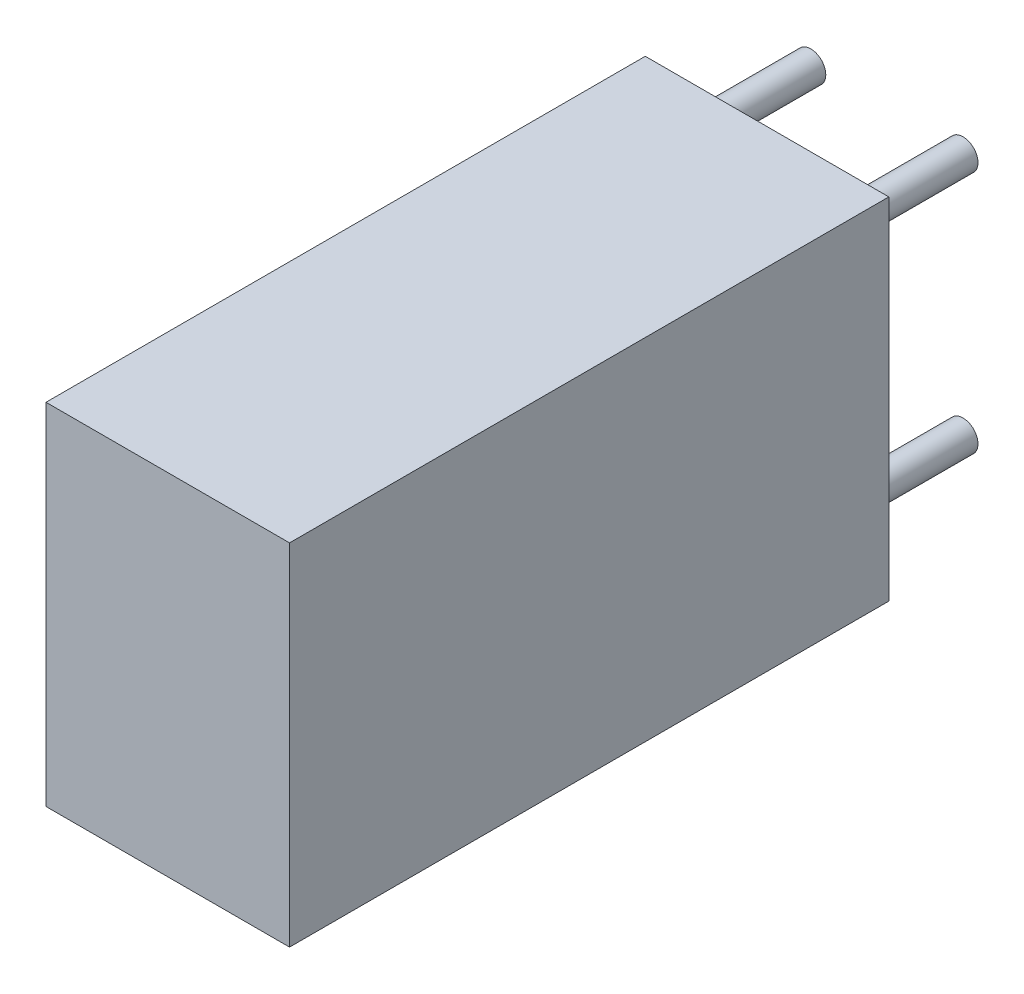
SolidWorks part; units mm, degrees
ref_plane "Front Plane" through (0, 0, 0) normal (0, 0, 1) x (1, 0, 0)
ref_plane "Top Plane" through (0, 0, 0) normal (0, 1, 0) x (1, 0, 0)
ref_plane "Right Plane" through (0, 0, 0) normal (1, 0, 0) x (0, 0, -1)
sketch "Sketch1" plane through (0, 0, 0) normal (0, 0, 1) x (1, 0, 0)
  line L0 (-0.762, 4.826) -> (-0.762, -1.016)
  line L1 (-0.762, -1.016) -> (3.302, -1.016)
  line L2 (3.302, -1.016) -> (3.302, 4.826)
  line L3 (3.302, 4.826) -> (-0.762, 4.826)
extrude "Component_Outline" add sketch "Sketch1" along normal blind 10 separate body
sketch "Sketch2" plane through (0, 0, 0) normal (0, 0, 1) x (1, 0, 0)
  circle A0 centre (0, 4.064) radius 0.25
extrude "1" add sketch "Sketch2" against normal blind 2 separate body
sketch "Sketch3" plane through (0, 0, 0) normal (0, 0, 1) x (1, 0, 0)
  circle A0 centre (2.54, 4.064) radius 0.25
extrude "2" add sketch "Sketch3" against normal blind 2 separate body
sketch "Sketch4" plane through (0, 0, 0) normal (0, 0, 1) x (1, 0, 0)
  circle A0 centre (2.54, 0) radius 0.25
extrude "3" add sketch "Sketch4" against normal blind 2 separate body
sketch "Sketch5" plane through (0, 0, 0) normal (0, 0, 1) x (1, 0, 0)
  circle A0 centre (0, 0) radius 0.25
extrude "4" add sketch "Sketch5" against normal blind 2 separate body
sketch3d "3DSketch1"
  line L0 (0, 0, 0) -> (1, 0, 0)
  line L1 (0, 0, 0) -> (0, 1, 0)
  line L2 (0, 0, 0) -> (0, 0, 1)
  point P0 (0, 0, 0)
